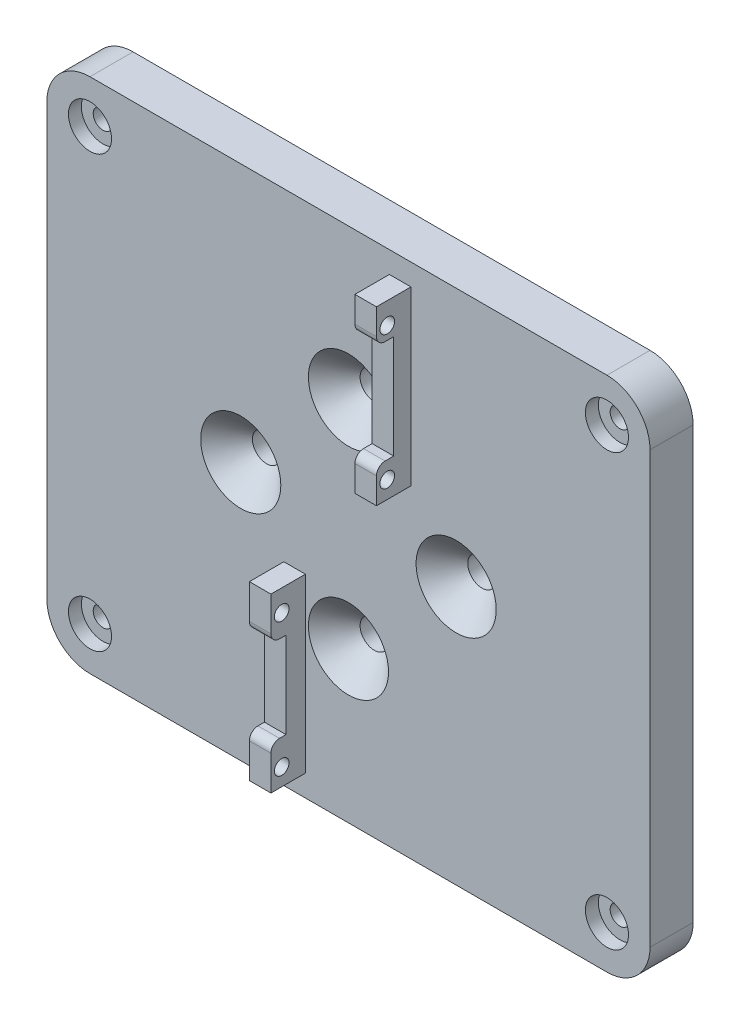
SolidWorks part; units mm, degrees
ref_plane "정면" through (0, 0, 0) normal (0, 0, 1) x (1, 0, 0)
ref_plane "윗면" through (0, 0, 0) normal (0, 1, 0) x (1, 0, 0)
ref_plane "우측면" through (0, 0, 0) normal (1, 0, 0) x (0, 0, -1)
sketch "스케치1" plane through (0, 0, 0) normal (0, 0, 1) x (1, 0, 0)
  line L0 (-70, 60) -> (-70, -60)
  line L1 (-70, 60) -> (70, 60)
  line L3 (-70, -60) -> (70, -60)
  line L5 (-70, 60) -> (70, -60) construction
  line L6 (-70, -60) -> (70, 60) construction
  line L7 (70, 60) -> (70, -60)
  point P0 (0, 0)
  dimension "D2" = 120
  dimension "D1" = 140
extrude "보스-돌출1" add sketch "스케치1" along normal blind 10
hole_wizard "M6 접시 머리 나사용 카운터싱크1" positions "스케치2" profile "스케치3" countersink size "M6" standard "ISO" end condition through all
sketch "스케치2" plane through (0, 0, 10) normal (0, 0, 1) x (1, 0, 0)
  circle A0 centre (0, 0) radius 25
  point P0 (0, 25)
  point P12 (25, 0)
  point P13 (0, -25)
  point P14 (-25, 0)
  dimension "D1" = 50
  dimension "D2" = 4
sketch "스케치3" plane through (0, 25, 10) normal (1, 0, 0) x (0, -1, 0)
  line L0 (0, 0) -> (0, 10)
  line L1 (0, 10) -> (3.3, 10)
  line L2 (3.3, 10) -> (3.3, 6)
  line L3 (3.3, 6) -> (9.3, 0)
  line L5 (9.3, 0) -> (0, 0)
  line L6 (-3.3, 6) -> (-9.3, 0) construction
  line L11 (0, -6.35) -> (0, 107.95) construction
  dimension "관통 구멍 지름" = 6.6
  dimension "관통 구멍 깊이" = 10
  dimension "표면 카운터싱크 지름" = 18.6
  dimension "표면 카운터싱크 각도" = 90
sketch "스케치4" plane through (0, 0, 10) normal (0, 0, 1) x (1, 0, 0)
  line L0 (0, 0) -> (0, -9.8201) construction
  line L5 (70, 60) -> (-70, 60) construction
  line L7 (-10, -55) -> (-15, -15) construction
  line L8 (-10, -15) -> (-15, -55) construction
  line L9 (-15, -15) -> (-15, -55)
  line L10 (-10, -55) -> (-15, -55)
  line L11 (-10, -15) -> (-10, -55)
  line L12 (-10, -15) -> (-15, -15)
  point P12 (-12.5, 0)
  dimension "D1" = 12.5
  dimension "D2" = 5
  dimension "D3" = 40
  dimension "D5" = 75
  dimension "D6" = 10
extrude "보스-돌출2" add sketch "스케치4" along normal blind 8
hole_wizard "M3 여유 구멍2" positions "스케치7" profile "스케치8" hole size "M3" standard "ISO" end condition up to next
sketch "스케치7" plane through (-10, 0, 0) normal (1, 0, 0) x (0, 0, -1)
  line L2 (-18, -15) -> (-10, -15) construction
  line L5 (-10, -60) -> (-10, 60) construction
  point P2 (-15.5, -51)
  point P4 (-15.5, -20)
  dimension "D1" = 5.5
  dimension "D2" = 5
  dimension "D4" = 31
sketch "스케치8" plane through (-10, -51, 15.5) normal (0, 1, 0) x (0, 0, -1)
  line L0 (0, 0) -> (0, 5)
  line L1 (0, 5) -> (1.7, 5)
  line L2 (1.7, 5) -> (1.7, 0)
  line L5 (1.7, 0) -> (0, 0)
  line L11 (0, -6.35) -> (0, 107.95) construction
  dimension "관통 구멍 지름" = 3.4
  dimension "관통 구멍 깊이" = 5
sketch "스케치13" plane through (0, 0, 10) normal (0, 0, 1) x (1, 0, 0)
  line L0 (0, 0) -> (0, 40.6112) construction
  line L1 (70, 60) -> (-70, 60) construction
  line L2 (-70, 60) -> (-70, -60) construction
  line L3 (0, 0) -> (8.135, 0) construction
  circle A0 centre (-60, 50) radius 5
  circle A1 centre (60, 50) radius 5
  circle A2 centre (60, -50) radius 5
  circle A3 centre (-60, -50) radius 5
  dimension "D2" = 10
  dimension "D3" = 10
  dimension "D1" = 10
extrude "컷-돌출5" cut sketch "스케치13" against normal blind 3
hole_wizard "M4 남비 머리 나사용 카운터보어1" positions "스케치16" profile "스케치17" counterbore size "M4" standard "ISO" end condition through all
sketch "스케치16" plane through (0, 0, 0) normal (0, 0, -1) x (-1, 0, 0)
  point P0 (-60, 50)
  point P3 (60, 50)
  point P6 (60, -50)
  point P9 (-60, -50)
sketch "스케치17" plane through (60, 50, 0) normal (1, 0, 0) x (0, 1, 0)
  line L0 (0, 0) -> (0, 18)
  line L1 (0, 18) -> (2.25, 18)
  line L3 (2.25, 18) -> (2.25, 3.1)
  line L4 (2.25, 3.1) -> (4.5, 3.1)
  line L5 (4.5, 3.1) -> (4.5, 0)
  line L7 (4.5, 0) -> (0, 0)
  line L11 (0, -6.35) -> (0, 107.95) construction
  dimension "관통 구멍 지름" = 4.5
  dimension "관통 구멍 깊이" = 18
  dimension "카운터보어 지름" = 9
  dimension "카운터보어 깊이" = 3.1
sketch "스케치21" plane through (0, 0, 10) normal (0, 0, 1) x (1, 0, 0)
  line L0 (70, -60) -> (70, 60) construction
  line L1 (9.5, 55) -> (14.5, 55)
  line L2 (9.5, 55) -> (9.5, 15)
  line L3 (9.5, 15) -> (14.5, 15)
  line L4 (14.5, 55) -> (14.5, 15)
  line L5 (9.5, 55) -> (14.5, 15) construction
  line L6 (9.5, 15) -> (14.5, 55) construction
  line L7 (70, 60) -> (-70, 60) construction
  point P0 (12, 35)
  dimension "D1" = 5
  dimension "D2" = 55.5
  dimension "D3" = 5
  dimension "D4" = 40
extrude "보스-돌출4" add sketch "스케치21" along normal blind 8
hole_wizard "M3 여유 구멍4" positions "스케치22" profile "스케치23" hole size "M3" standard "ISO" end condition through all
sketch "스케치22" plane through (9.5, 0, 0) normal (-1, 0, 0) x (0, 0, 1)
  line L0 (10, 55) -> (10, 15) construction
  line L1 (18, 55) -> (10, 55) construction
  point P0 (15.5, 50)
  point P2 (15.5, 19)
  dimension "D1" = 5.5
  dimension "D2" = 5
  dimension "D3" = 31
sketch "스케치23" plane through (9.5, 50, 15.5) normal (0, 1, 0) x (0, 0, 1)
  line L0 (0, 0) -> (0, 60.5)
  line L1 (0, 60.5) -> (1.7, 60.5)
  line L2 (1.7, 60.5) -> (1.7, 0)
  line L5 (1.7, 0) -> (0, 0)
  line L11 (0, -6.35) -> (0, 107.95) construction
  dimension "관통 구멍 지름" = 3.4
  dimension "관통 구멍 깊이" = 60.5
sketch "스케치24" plane through (-10, 0, 0) normal (1, 0, 0) x (0, 0, -1)
  line L0 (-18, -55) -> (-18, -15) construction
  line L1 (-18, -25) -> (-14.5, -25)
  line L2 (-18, -25) -> (-18, -45)
  line L3 (-18, -45) -> (-14.5, -45)
  line L4 (-14.5, -25) -> (-14.5, -45)
  line L5 (-18, -25) -> (-14.5, -45) construction
  line L6 (-18, -45) -> (-14.5, -25) construction
  line L7 (-18, 15) -> (-18, 55) construction
  line L8 (-18, 47) -> (-14, 47)
  line L9 (-18, 47) -> (-18, 23)
  line L10 (-18, 23) -> (-14, 23)
  line L11 (-14, 47) -> (-14, 23)
  line L12 (-18, 47) -> (-14, 23) construction
  line L13 (-18, 23) -> (-14, 47) construction
  point P0 (-16.25, -35)
  point P7 (-18, -35)
  point P8 (-16, 35)
  point P15 (-18, 35)
  point P17 (-18, 35)
  dimension "D1" = 20
  dimension "D2" = 3.5
  dimension "D3" = 24
  dimension "D4" = 4
extrude "컷-돌출6" cut sketch "스케치24" against normal through all both and the other way through all
fillet "필렛1" radius 10 4 edges at (-70, 60, 5) (-70, -60, 5) (70, -60, 5) (70, 60, 5)
fillet "필렛2" radius 2 4 edges at (12, 47, 18) (-12.5, -45, 18) (-12.5, -25, 18) (12, 23, 18)
